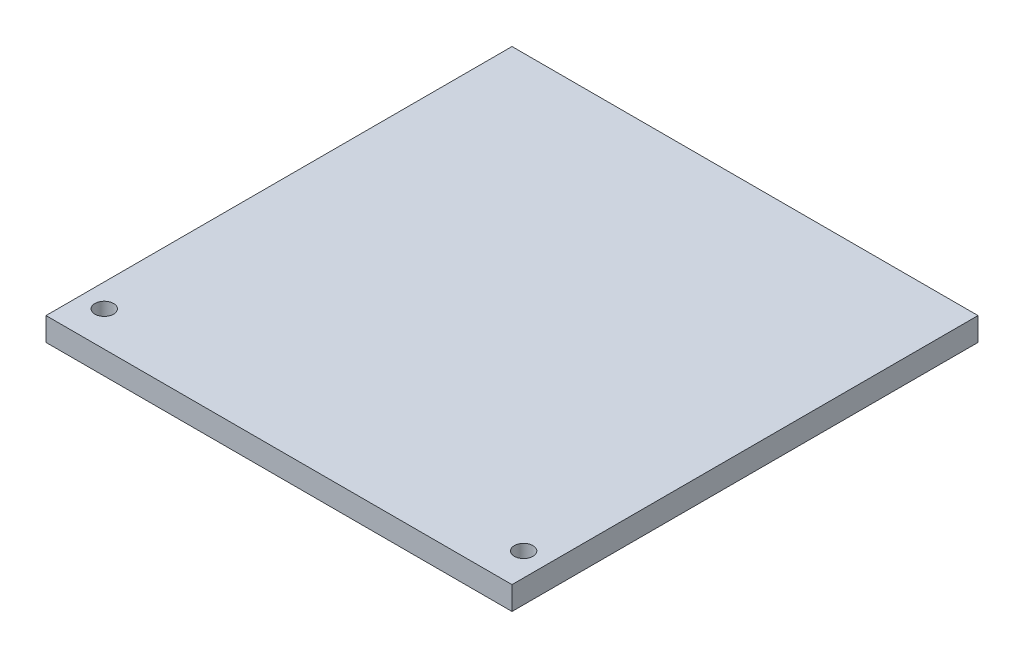
SolidWorks part; units mm, degrees
material "Plain Carbon Steel"
ref_plane "Front Plane" through (0, 0, 0) normal (0, 0, 1) x (1, 0, 0)
ref_plane "Top Plane" through (0, 0, 0) normal (0, 1, 0) x (1, 0, 0)
ref_plane "Right Plane" through (0, 0, 0) normal (1, 0, 0) x (0, 0, -1)
sketch "Sketch1" plane through (0, 0, 0) normal (0, 1, 0) x (1, 0, 0)
  line L1 (-100, -100) -> (100, -100)
  line L2 (-100, -100) -> (-100, 100)
  line L3 (-100, 100) -> (100, 100)
  line L4 (100, -100) -> (100, 100)
  line L5 (-100, -100) -> (100, 100) construction
  line L6 (-100, 100) -> (100, -100) construction
  point P0 (0, 0)
  dimension "D1" = 200
  dimension "D2" = 200
extrude "Boss-Extrude1" add sketch "Sketch1" along normal blind 10
sketch "Sketch2" plane through (0, 10, 0) normal (0, 1, 0) x (1, 0, 0)
  line L0 (-100, -100) -> (100, -100) construction
  line L1 (-100, 100) -> (-100, -100) construction
  line L2 (100, -100) -> (100, 100) construction
  circle A0 centre (-90, -85) radius 4
  circle A1 centre (90, -85) radius 4
  dimension "D3" = 8
  dimension "D1" = 15
  dimension "D2" = 10
  dimension "D4" = 10
extrude "Cut-Extrude1" cut sketch "Sketch2" against normal blind 10
